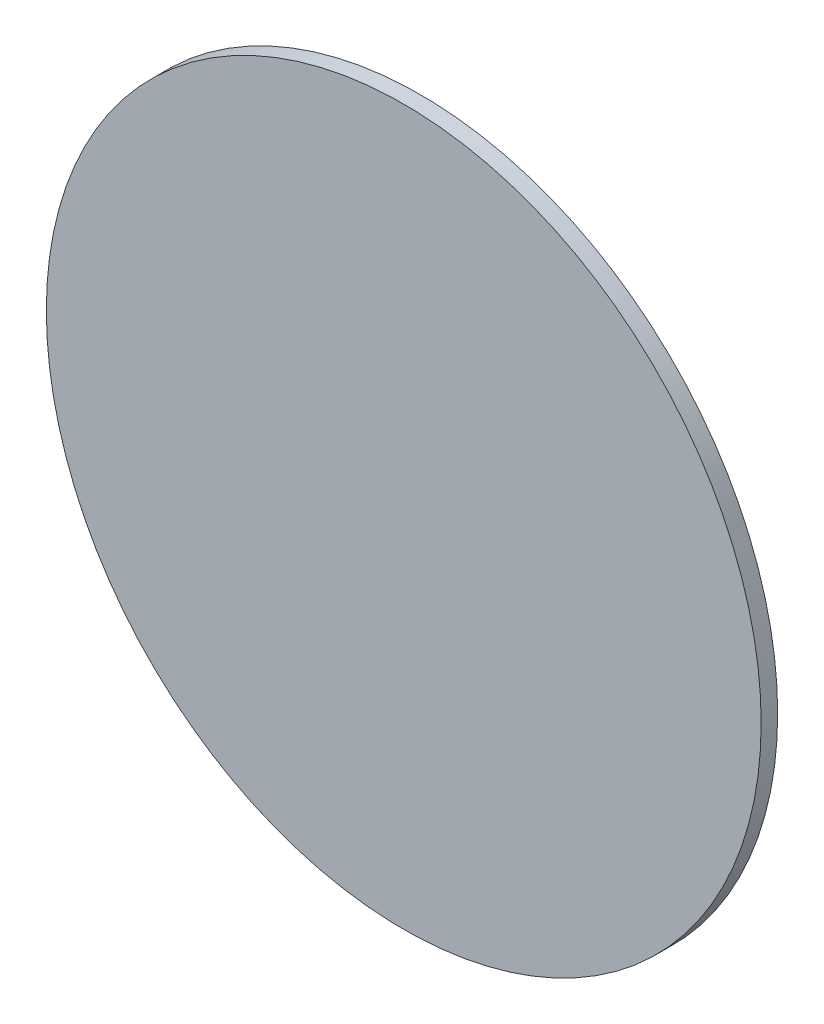
SolidWorks part; units mm, degrees
ref_plane "Спереди" through (0, 0, 0) normal (0, 0, 1) x (1, 0, 0)
ref_plane "Сверху" through (0, 0, 0) normal (0, 1, 0) x (1, 0, 0)
ref_plane "Справа" through (0, 0, 0) normal (1, 0, 0) x (0, 0, -1)
sketch "Эскиз1" plane through (0, 0, 0) normal (0, 0, 1) x (1, 0, 0)
  circle A0 centre (0, 0) radius 11.5
  circle A1 centre (0, 0) radius 11 construction
  circle A2 centre (0, 0) radius 16
  circle A3 centre (0, 0) radius 16 construction
  dimension "D1" = 0.5
extrude "Бобышка-Вытянуть1" add sketch "Эскиз1" along normal blind 19
sketch "Эскиз2" plane through (0, 0, 19) normal (0, 0, 1) x (1, 0, 0)
  circle A0 centre (0, 0) radius 65
  dimension "D1" = 130
extrude "Бобышка-Вытянуть2" add sketch "Эскиз2" along normal blind 3
